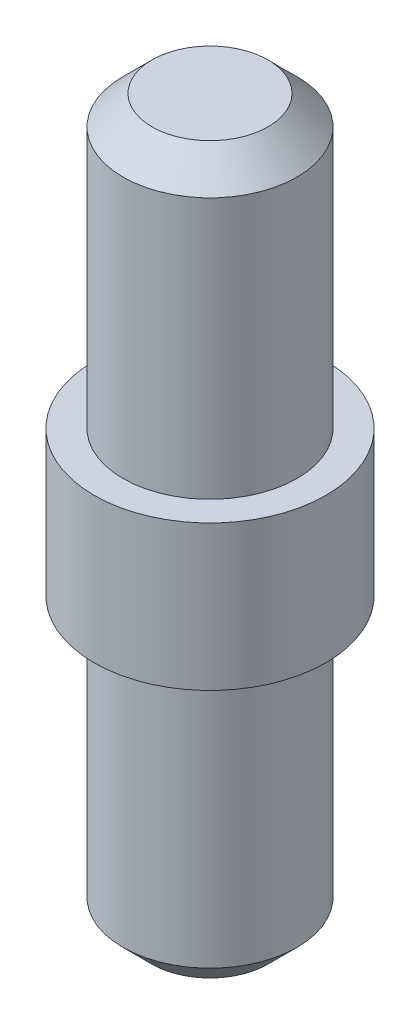
SolidWorks part; units mm, degrees
ref_plane "前基準面" through (0, 0, 0) normal (0, 0, 1) x (1, 0, 0)
ref_plane "上基準面" through (0, 0, 0) normal (0, 1, 0) x (1, 0, 0)
ref_plane "右基準面" through (0, 0, 0) normal (1, 0, 0) x (0, 0, -1)
sketch "草圖1" plane through (0, 0, 0) normal (0, 0, 1) x (1, 0, 0)
  line L0 (0, 66.7583) -> (0, -59.0257) construction
  line L1 (2, 25) -> (3, 24)
  line L2 (0, 25) -> (2, 25)
  line L5 (3, 24) -> (3, 15)
  line L6 (3, 15) -> (4, 15)
  line L8 (3, 10) -> (4, 10)
  line L9 (4, 15) -> (4, 10)
  line L12 (0, 0) -> (2, 0)
  line L13 (3, 10) -> (3, 1)
  line L14 (3, 1) -> (2, 0)
  line L15 (0, 25) -> (0, 0)
  point P6 (3, 25)
  point P10 (3, 0)
  dimension "D1" = 8
  dimension "D2" = 6
  dimension "D5" = 5
  dimension "D6" = 10
  dimension "D7" = 10
revolve "旋轉1" add sketch "草圖1" angle 360 about L0
